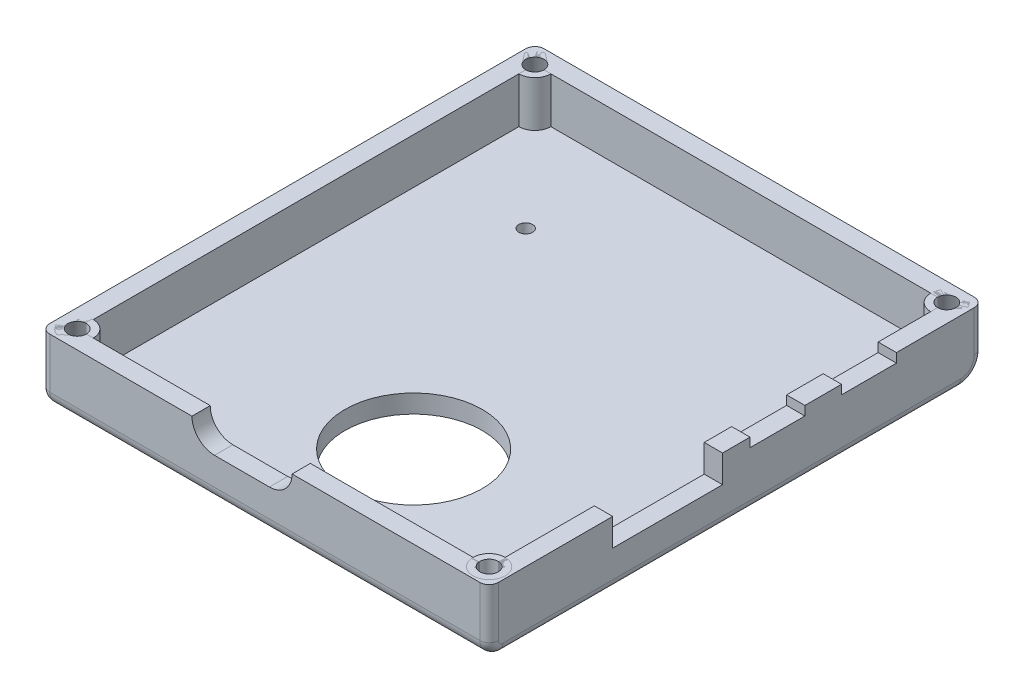
SolidWorks part; units mm, degrees
ref_plane "Front Plane" through (0, 0, 0) normal (0, 0, 1) x (1, 0, 0)
ref_plane "Top Plane" through (0, 0, 0) normal (0, 1, 0) x (1, 0, 0)
ref_plane "Right Plane" through (0, 0, 0) normal (1, 0, 0) x (0, 0, -1)
sketch "Sketch1" plane through (0, 0, 0) normal (0, 1, 0) x (1, 0, 0)
  line L1 (24.5, 27) -> (-24.5, 27)
  line L2 (24.5, 27) -> (24.5, -27)
  line L3 (24.5, -27) -> (-24.5, -27)
  line L4 (-24.5, 27) -> (-24.5, -27)
  line L5 (24.5, 27) -> (-24.5, -27) construction
  line L6 (24.5, -27) -> (-24.5, 27) construction
  point P0 (0, 0)
  dimension "D1" = 49
  dimension "D2" = 54
extrude "Boss-Extrude1" add sketch "Sketch1" along normal blind 2
sketch "Sketch2" plane through (0, 2, 0) normal (0, 1, 0) x (1, 0, 0)
  line L1 (24.5, 27) -> (-24.5, 27)
  line L2 (24.5, 27) -> (24.5, -27)
  line L3 (24.5, -27) -> (-24.5, -27)
  line L4 (-24.5, 27) -> (-24.5, -27)
  line L5 (24.5, 27) -> (-24.5, -27) construction
  line L6 (24.5, -27) -> (-24.5, 27) construction
  point P0 (0, 0)
extrude "Extrude-Thin1" add sketch "Sketch2" along normal blind 5 thin thin type one direction reverse wall 2
sketch "Sketch3" plane through (24.5, 0, 0) normal (1, 0, 0) x (0, 0, -1)
  line L0 (-27, 7) -> (-13.5, 7)
  line L1 (-27, 7) -> (27, 7) construction
  line L2 (-13.5, 7) -> (-1.5, 7)
  line L3 (-1.5, 7) -> (-1.5, 4)
  line L4 (-1.5, 4) -> (-13.5, 4)
  line L5 (-13.5, 4) -> (-13.5, 7)
  dimension "D1" = 13.5
  dimension "D2" = 12
  dimension "D3" = 3
extrude "Cut-Extrude4" cut sketch "Sketch3" against normal blind 2 contours L2 L3 L4 L5
sketch "Sketch9" plane through (24.5, 0, 0) normal (1, 0, 0) x (0, 0, -1)
  line L0 (-1.5, 7) -> (1.5, 7)
  line L1 (25, 7) -> (-25, 7) construction
  line L2 (1.5, 7) -> (7.5, 7)
  line L3 (-1.5, 7) -> (27, 7) construction
  line L4 (7.5, 7) -> (11.5, 7)
  line L5 (11.5, 7) -> (17.5, 7)
  dimension "D1" = 3
  dimension "D2" = 6
  dimension "D3" = 4
  dimension "D4" = 6
sketch "Sketch10" plane through (24.5, 0, 0) normal (1, 0, 0) x (0, 0, -1)
  line L0 (1.5, 7) -> (7.5, 7)
  line L1 (7.5, 7) -> (7.5, 6)
  line L2 (7.5, 6) -> (1.5, 6)
  line L3 (1.5, 6) -> (1.5, 7)
  dimension "D1" = 1
sketch "Sketch11" plane through (24.5, 0, 0) normal (1, 0, 0) x (0, 0, -1)
  line L0 (17.5, 7) -> (11.5, 7)
  line L1 (11.5, 7) -> (11.5, 6)
  line L2 (11.5, 6) -> (17.5, 6)
  line L3 (17.5, 6) -> (17.5, 7)
  dimension "D1" = 1
extrude "Cut-Extrude5" cut sketch "Sketch10" against normal blind 2
extrude "Cut-Extrude6" cut sketch "Sketch11" against normal blind 2
sketch "Sketch14" plane through (0, 0, 0) normal (0, -1, 0) x (1, 0, 0)
  line L0 (24.5, 27) -> (2.25, 27)
  line L1 (-24.5, 27) -> (24.5, 27) construction
  line L2 (2.25, 27) -> (2.25, 13)
  dimension "D1" = 22.25
  dimension "D2" = 14
sketch "Sketch16" plane through (0, 0, 0) normal (0, -1, 0) x (1, 0, 0)
  circle A0 centre (2.25, 13) radius 7.5
extrude "Cut-Extrude7" cut sketch "Sketch16" against normal blind 2
sketch "Sketch18" plane through (0, 0, 27) normal (0, 0, 1) x (1, 0, 0)
  line L0 (24.5, 7) -> (3, 7)
  line L1 (-24.5, 7) -> (24.5, 7) construction
  dimension "D1" = 21.5
sketch "Sketch21" plane through (0, 0, 27) normal (0, 0, 1) x (1, 0, 0)
  line L0 (3, 7) -> (0.5, 7)
  line L1 (-24.5, 7) -> (24.5, 7) construction
  line L2 (0.5, 7) -> (-5.5, 7)
  line L3 (-5.5, 7) -> (-8, 7)
  line L4 (3, 7) -> (3, 5)
  line L5 (3, 5) -> (-8, 5)
  line L6 (-8, 5) -> (-8, 7)
  dimension "D1" = 2.5
  dimension "D2" = 6
  dimension "D3" = 2.5
  dimension "D4" = 2
sketch "Sketch22" plane through (0, 0, 27) normal (0, 0, 1) x (1, 0, 0)
  line L0 (0.5, 7) -> (-5.5, 7) construction
  line L1 (0.5, 4.5297) -> (-5.5, 4.5297)
  line L2 (0.5, 9.4703) -> (-5.5, 9.4703)
  arc A0 (0.5, 4.5297) -> (0.5, 9.4703) centre (0.5, 7) ccw
  arc A1 (-5.5, 9.4703) -> (-5.5, 4.5297) centre (-5.5, 7) ccw
  point P4 (-2.5, 7)
extrude "Cut-Extrude8" cut sketch "Sketch22" against normal blind 2
sketch "Sketch23" plane through (0, 0, 0) normal (0, -1, 0) x (1, 0, 0)
  line L0 (24.5, 27) -> (-12.5, 27)
  line L1 (-24.5, 27) -> (24.5, 27) construction
  line L2 (-12.5, 27) -> (-12.5, -14)
  dimension "D1" = 37
  dimension "D2" = 41
sketch "Sketch24" plane through (0, 0, 0) normal (0, -1, 0) x (1, 0, 0)
  circle A0 centre (-12.5, -14) radius 0.75
extrude "Cut-Extrude9" cut sketch "Sketch24" against normal blind 2
sketch "Sketch26" plane through (0, 2, 0) normal (0, 1, 0) x (1, 0, 0)
  circle A0 centre (-22.5, 25) radius 1.75
  circle A1 centre (22.5, 25) radius 1.75
  circle A2 centre (22.5, -25) radius 1.75
  circle A3 centre (-22.5, -25) radius 1.75
extrude "Boss-Extrude2" add sketch "Sketch26" along normal blind 5 separate body
sketch "Sketch27" plane through (0, 2, 0) normal (0, 1, 0) x (1, 0, 0)
  circle A0 centre (-22.5, 25) radius 1
  circle A1 centre (22.5, 25) radius 1
  circle A2 centre (22.5, -25) radius 1
  circle A3 centre (-22.5, -25) radius 1
extrude "Cut-Extrude10" cut sketch "Sketch27" along normal blind 5
fillet "Fillet3" radius 1.5 1 edges at (0, 0, 27)
fillet "Fillet4" radius 2.5 1 edges at (0, 0, -27)
fillet "Fillet5" radius 1 10 edges at (24.5, 0.4393, 26.5607) (24.5, 0, 0.5) (24.5, 0.7322, -26.2678) (-24.5, 0.7322, -26.2678) (-24.5, 0, 0.5) (-24.5, 0.4393, 26.5607) (24.5, 4.25, 27) (24.5, 4.75, -27) (-24.5, 4.75, -27) (-24.5, 4.25, 27)
